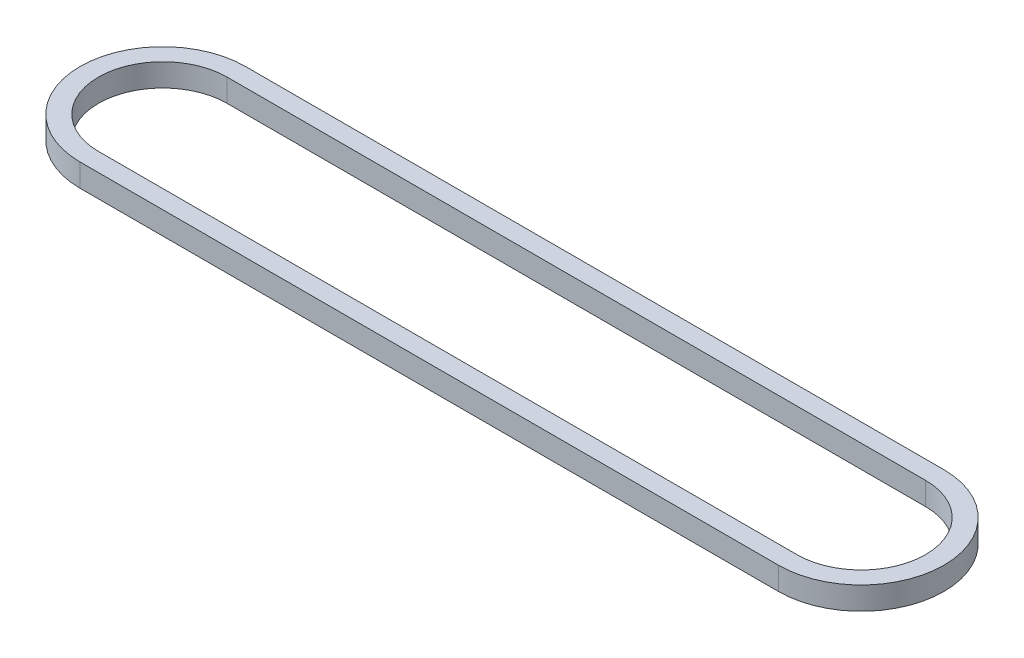
SolidWorks part; units mm, degrees
ref_plane "Front Plane" through (0, 0, 0) normal (0, 0, 1) x (1, 0, 0)
ref_plane "Top Plane" through (0, 0, 0) normal (0, 1, 0) x (1, 0, 0)
ref_plane "Right Plane" through (0, 0, 0) normal (1, 0, 0) x (0, 0, -1)
sketch "Sketch1" plane through (0, 0, 0) normal (0, 1, 0) x (1, 0, 0)
  line L0 (0, 0) -> (241.3, 0) construction
  line L1 (0, 22.225) -> (241.3, 22.225)
  line L2 (0, -22.225) -> (241.3, -22.225)
  line L3 (0, 28.575) -> (241.3, 28.575)
  line L4 (0, -28.575) -> (241.3, -28.575)
  arc A0 (0, 22.225) -> (0, -22.225) centre (0, 0) ccw
  arc A1 (241.3, -22.225) -> (241.3, 22.225) centre (241.3, 0) ccw
  arc A2 (241.3, -28.575) -> (241.3, 28.575) centre (241.3, 0) ccw
  arc A3 (0, 28.575) -> (0, -28.575) centre (0, 0) ccw
  point P3 (120.65, 0)
  dimension "D2" = 22.225
  dimension "D1" = 241.3
  dimension "D3" = 6.35
extrude "Boss-Extrude1" add sketch "Sketch1" along normal blind 7.874
